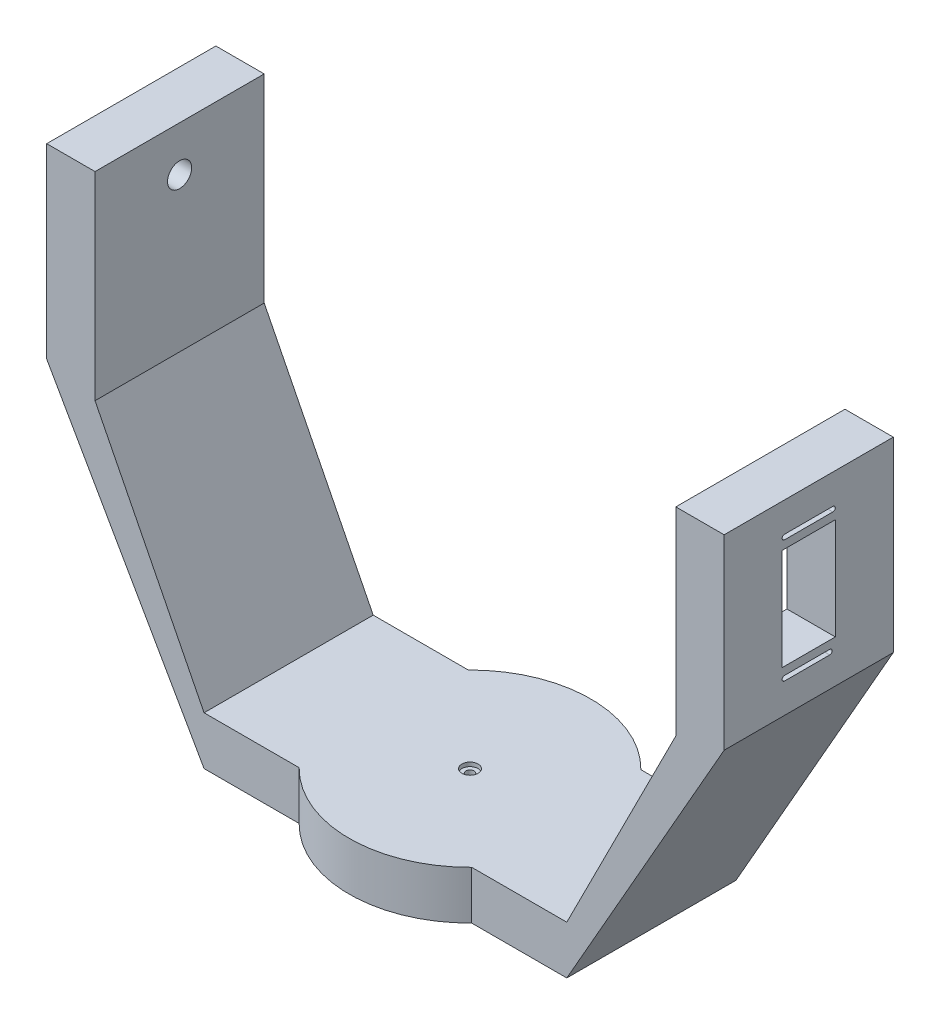
SolidWorks part; units mm, degrees
ref_plane "Front" through (0, 0, 0) normal (0, 0, 1) x (1, 0, 0)
ref_plane "Top" through (0, 0, 0) normal (0, 1, 0) x (1, 0, 0)
ref_plane "Right" through (0, 0, 0) normal (1, 0, 0) x (0, 0, -1)
sketch "草图1" plane through (0, 0, 0) normal (0, 1, 0) x (1, 0, 0)
  line L13 (0.0555, 35) -> (75.0555, 35)
  line L14 (0.0555, 35) -> (0.0555, -35)
  line L15 (0.0555, -35) -> (75.0555, -35)
  line L16 (75.0555, 35) -> (75.0555, -35)
  circle A1 centre (0, 0) radius 50
  dimension "D1" = 100
  dimension "D2" = 35
  dimension "D3" = 35
  dimension "D4" = 75
extrude "凸台-拉伸1" add sketch "草图1" along normal blind 20 contours A1 L15 L16 L13 | L15 A1 L13 L14 | L13 A1 L15 L14
sketch "草图2" plane through (0, 0, 35) normal (0, 0, 1) x (1, 0, 0)
  line L0 (75.0555, 0) -> (140.1741, 114.1921)
  line L1 (140.1741, 114.1921) -> (140.1741, 191.4116)
  line L2 (140.1741, 191.4116) -> (120.1741, 191.4116)
  line L3 (120.1741, 191.4116) -> (120.1741, 109.2863)
  line L5 (120.1741, 109.2863) -> (75.0555, 20)
  line L6 (75.0555, 20) -> (75.0555, 0)
  dimension "D1" = 20
  dimension "D2" = 77.2194
extrude "凸台-拉伸2" add sketch "草图2" against normal blind 70 contours L2 L3 L5 L6 L0 L1
mirror "镜向1" about plane through (0, 0, 0) normal (1, 0, 0) of "凸台-拉伸1", "凸台-拉伸2"
hole_wizard "1/4 六角头螺钉的柱形沉头孔base" positions "草图7" profile "草图8" counterbore size "M3" standard "ANSI Metric" end condition through all
sketch "草图7" plane through (0, 20, 0) normal (0, 1, 0) x (1, 0, 0)
  point P0 (0, 0)
sketch "草图8" plane through (0, 20, 0) normal (1, 0, 0) x (0, 0, 1)
  line L0 (0, 0) -> (0, 20)
  line L1 (0, 20) -> (1.7, 20)
  line L3 (1.7, 20) -> (1.7, 1.65)
  line L4 (1.7, 1.65) -> (3.35, 1.65)
  line L5 (3.35, 1.65) -> (3.35, 0)
  line L7 (3.35, 0) -> (0, 0)
  line L11 (0, -6.35) -> (0, 107.95) construction
  dimension "通孔孔直径" = 3.4
  dimension "通孔孔深度" = 20
  dimension "柱形沉头孔直径" = 6.7
  dimension "柱形沉头孔深度" = 1.65
sketch "草图10" plane through (0, 0, 35) normal (0, 0, 1) x (1, 0, 0)
sketch "草图11" plane through (140.1741, 0, 0) normal (1, 0, 0) x (0, 0, -1)
  line L1 (-11, 173.8016) -> (11, 173.8016)
  line L2 (-11, 173.8016) -> (-11, 131.8016)
  line L3 (-11, 131.8016) -> (11, 131.8016)
  line L4 (11, 173.8016) -> (11, 131.8016)
  line L5 (-35, 114.1921) -> (-35, 191.4116) construction
  line L7 (35, 191.4116) -> (-35, 191.4116) construction
  dimension "D1" = 22
  dimension "D2" = 42
  dimension "D3" = 24
  dimension "D4" = 17.61
extrude "切除-拉伸1" cut sketch "草图11" against normal blind 32
sketch "草图14" plane through (140.1741, 0, 0) normal (1, 0, 0) x (0, 0, -1)
  line L0 (-10, 179.1016) -> (10, 179.1016)
  line L1 (-10, 177.1016) -> (10, 177.1016)
  line L2 (11, 173.8016) -> (-11, 173.8016) construction
  line L3 (-35, 114.1921) -> (-35, 191.4116) construction
  line L6 (-10, 128.5016) -> (8.7063, 128.5016)
  line L7 (-10, 126.5016) -> (8.7063, 126.5016)
  line L8 (-11, 131.8016) -> (11, 131.8016) construction
  arc A0 (-10, 179.1016) -> (-10, 177.1016) centre (-10, 178.1016) ccw
  arc A1 (10, 179.1016) -> (10, 177.1016) centre (10, 178.1016) cw
  arc A4 (-10, 128.5016) -> (-10, 126.5016) centre (-10, 127.5016) ccw
  arc A5 (8.7063, 128.5016) -> (8.7063, 126.5016) centre (8.7063, 127.5016) cw
  dimension "D3" = 25
  dimension "D4" = 3.3
  dimension "D1" = 2
  dimension "D2" = 3.3
  dimension "D5" = 25
extrude "切除-拉伸2" cut sketch "草图14" against normal blind 67
sketch "草图15" plane through (-140.1741, 0, 0) normal (-1, 0, 0) x (0, 0, 1)
  line L0 (-35, 191.4116) -> (35, 191.4116) construction
  line L1 (-35, 114.1921) -> (-35, 191.4116) construction
  circle A0 centre (0, 172.8016) radius 5
  dimension "D3" = 10
  dimension "D1" = 18.61
  dimension "D2" = 35
extrude "切除-拉伸3" cut sketch "草图15" against normal blind 70
sketch "草图16" plane through (0, 0, 0) normal (0, -1, 0) x (1, 0, 0)
  line L0 (-30, 3) -> (0.7849, 6.6456)
  line L2 (0.7849, -6.6456) -> (-30, -3)
  line L4 (-35.7071, 35) -> (-75.0555, 35) construction
  line L8 (0.7849, 6.6456) -> (31.5445, 2.7923)
  line L9 (0.7849, -6.6456) -> (31.5445, -3)
  arc A1 (-30, 3) -> (-30, -3) centre (-30, 0) ccw
  arc A3 (31.5445, 2.7923) -> (31.5445, -3) centre (30.2173, -0.1038) cw
  dimension "D1" = 30
  dimension "D2" = 3
  dimension "D3" = 31
  dimension "D4" = 35
  dimension "D5" = 31
  dimension "D6" = 31
extrude "切除-拉伸4" cut sketch "草图16" against normal blind 2
sketch "草图17" plane through (0, 0, 0) normal (0, -1, 0) x (1, 0, 0)
  line L0 (0.7849, 6.6456) -> (-9.6422, 5.4108)
  line L1 (0.7849, 6.6456) -> (-30, 3) construction
  line L2 (-9.6422, 5.4108) -> (-9.6422, -5.4108)
  line L3 (-30, -3) -> (0.7849, -6.6456) construction
  line L4 (-9.6422, -5.4108) -> (0.7849, -6.6456)
  line L5 (0.7849, -6.6456) -> (11.2035, -5.4108)
  line L6 (0.7849, -6.6456) -> (31.5445, -3) construction
  line L7 (11.2035, -5.4108) -> (11.2035, 5.3404)
  line L8 (31.5445, 2.7923) -> (0.7849, 6.6456) construction
  line L9 (11.2035, 5.3404) -> (0.7849, 6.6456)
  dimension "D1" = 10.5
  dimension "D2" = 10.5
extrude "切除-拉伸5" cut sketch "草图17" against normal blind 3.5
